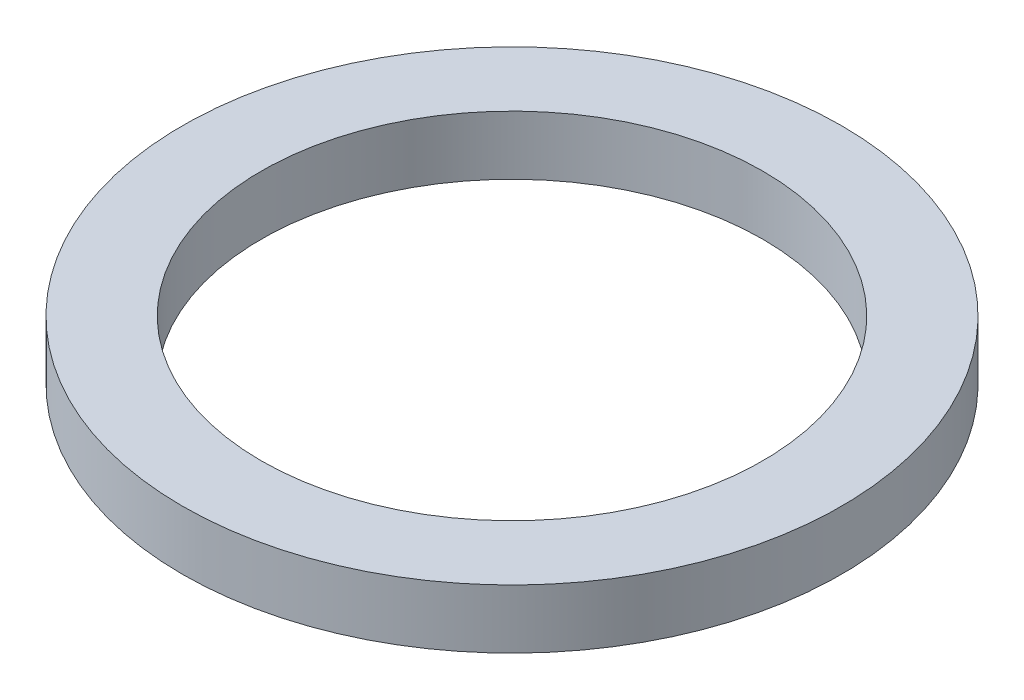
SolidWorks part; units mm, degrees
ref_plane "Front Plane" through (0, 0, 0) normal (0, 0, 1) x (1, 0, 0)
ref_plane "Top Plane" through (0, 0, 0) normal (0, 1, 0) x (1, 0, 0)
ref_plane "Right Plane" through (0, 0, 0) normal (1, 0, 0) x (0, 0, -1)
sketch "Sketch2" plane through (0, 0, 0) normal (0, 1, 0) x (1, 0, 0)
  circle A0 centre (0, 0) radius 4.2545
  circle A1 centre (0, 0) radius 3.2385
  dimension "D1" = 1.016
  dimension "D2" = 6.477
extrude "Boss-Extrude1" add sketch "Sketch2" along normal blind 0.762
